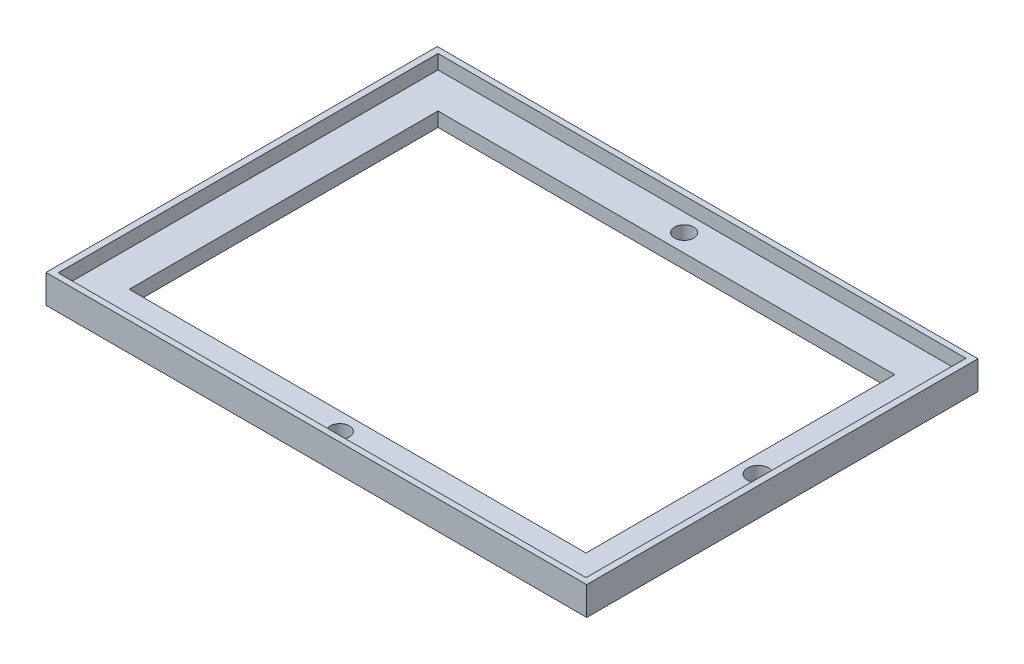
SolidWorks part; units mm, degrees
ref_plane "Front Plane" through (0, 0, 0) normal (0, 0, 1) x (1, 0, 0)
ref_plane "Top Plane" through (0, 0, 0) normal (0, 1, 0) x (1, 0, 0)
ref_plane "Right Plane" through (0, 0, 0) normal (1, 0, 0) x (0, 0, -1)
sketch "Sketch1" plane through (0, 0, 0) normal (0, 1, 0) x (1, 0, 0)
  line L1 (-38, 27.5) -> (38, 27.5)
  line L2 (-38, 27.5) -> (-38, -27.5)
  line L3 (-38, -27.5) -> (38, -27.5)
  line L4 (38, 27.5) -> (38, -27.5)
  line L5 (-38, 27.5) -> (38, -27.5) construction
  line L6 (-38, -27.5) -> (38, 27.5) construction
  line L7 (-32.1, 21.7) -> (32.1, 21.7)
  line L8 (-32.1, 21.7) -> (-32.1, -21.7)
  line L9 (-32.1, -21.7) -> (32.1, -21.7)
  line L10 (32.1, 21.7) -> (32.1, -21.7)
  line L11 (-32.1, 21.7) -> (32.1, -21.7) construction
  line L12 (-32.1, -21.7) -> (32.1, 21.7) construction
  point P0 (0, 0)
  point P6 (0, 0)
  dimension "D1" = 76
  dimension "D2" = 55
  dimension "D3" = 64.2
  dimension "D4" = 43.4
extrude "Boss-Extrude1" add sketch "Sketch1" along normal blind 4
sketch "Sketch2" plane through (0, 4, 0) normal (0, 1, 0) x (1, 0, 0)
  line L0 (32.1, 21.7) -> (-32.1, 21.7) construction
  line L1 (-37.1, 26.7) -> (37.1, 26.7)
  line L2 (-37.1, 26.7) -> (-37.1, -26.7)
  line L3 (-37.1, -26.7) -> (37.1, -26.7)
  line L4 (37.1, 26.7) -> (37.1, -26.7)
  line L5 (-37.1, 26.7) -> (37.1, -26.7) construction
  line L6 (-37.1, -26.7) -> (37.1, 26.7) construction
  line L7 (-32.1, 21.7) -> (-32.1, -21.7) construction
  point P0 (0, 0)
  dimension "D1" = 5
  dimension "D2" = 5
extrude "Cut-Extrude1" cut sketch "Sketch2" against normal blind 2
sketch "Sketch3" plane through (0, 2, 0) normal (0, 1, 0) x (1, 0, 0)
  line L0 (32.1, 21.7) -> (-32.1, 21.7) construction
  line L1 (0, 0) -> (4.8315, 0) construction
  circle A0 centre (0, 24.2) radius 1.35
  circle A1 centre (0, -24.2) radius 1.35
  dimension "D1" = 2.5
  dimension "D2" = 2.7
extrude "Cut-Extrude2" cut sketch "Sketch3" against normal blind 2
sketch "Sketch4" plane through (0, 2, 0) normal (0, 1, 0) x (1, 0, 0)
  line L0 (32.1, -21.7) -> (32.1, 21.7) construction
  circle A0 centre (34.6, 0) radius 1.5
  dimension "D1" = 3
  dimension "D2" = 2.5
extrude "Cut-Extrude3" cut sketch "Sketch4" against normal up to next
